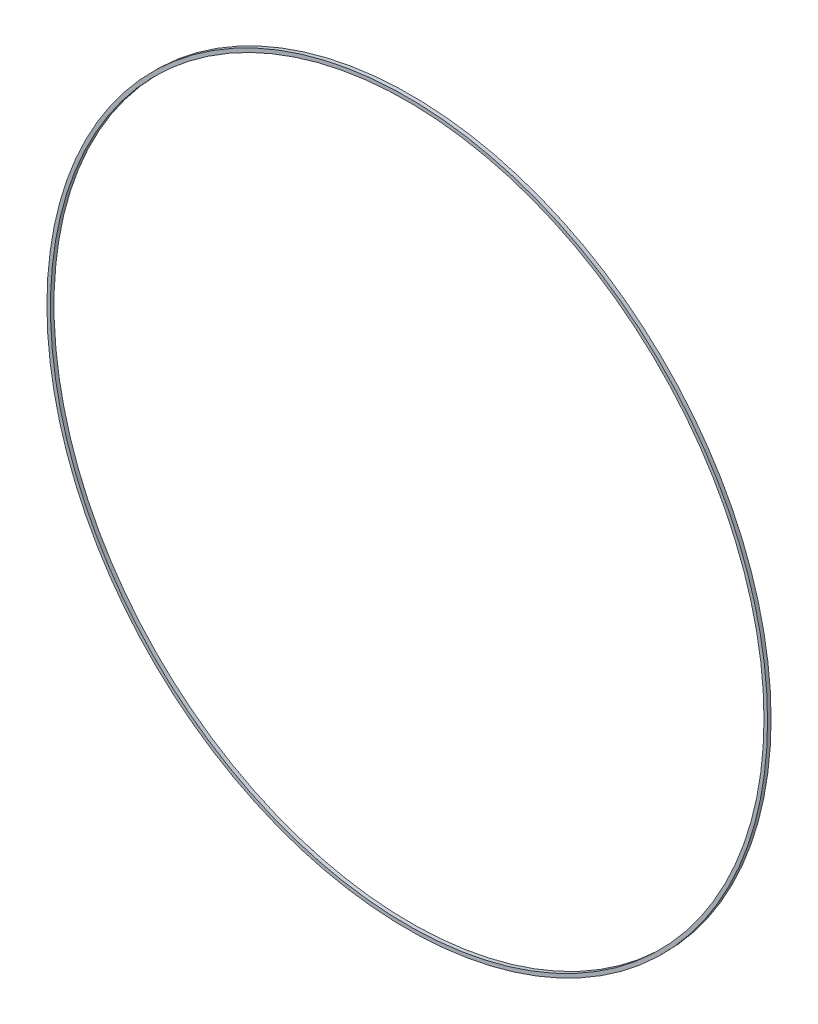
SolidWorks part; units mm, degrees
ref_plane "Front Plane" through (0, 0, 0) normal (0, 0, 1) x (1, 0, 0)
ref_plane "Top Plane" through (0, 0, 0) normal (0, 1, 0) x (1, 0, 0)
ref_plane "Right Plane" through (0, 0, 0) normal (1, 0, 0) x (0, 0, -1)
sketch "Sketch2" plane through (0, 0, 0) normal (0, 0, 1) x (1, 0, 0)
  circle A0 centre (0, 0) radius 203
  circle A1 centre (0, 0) radius 201
extrude "Boss-Extrude1" add sketch "Sketch2" along normal blind 2 contours A0
sketch "Sketch3" plane through (0, 0, 2) normal (0, 0, 1) x (1, 0, 0)
  circle A0 centre (0, 0) radius 201
extrude "Cut-Extrude1" cut sketch "Sketch3" against normal through all contours A0
